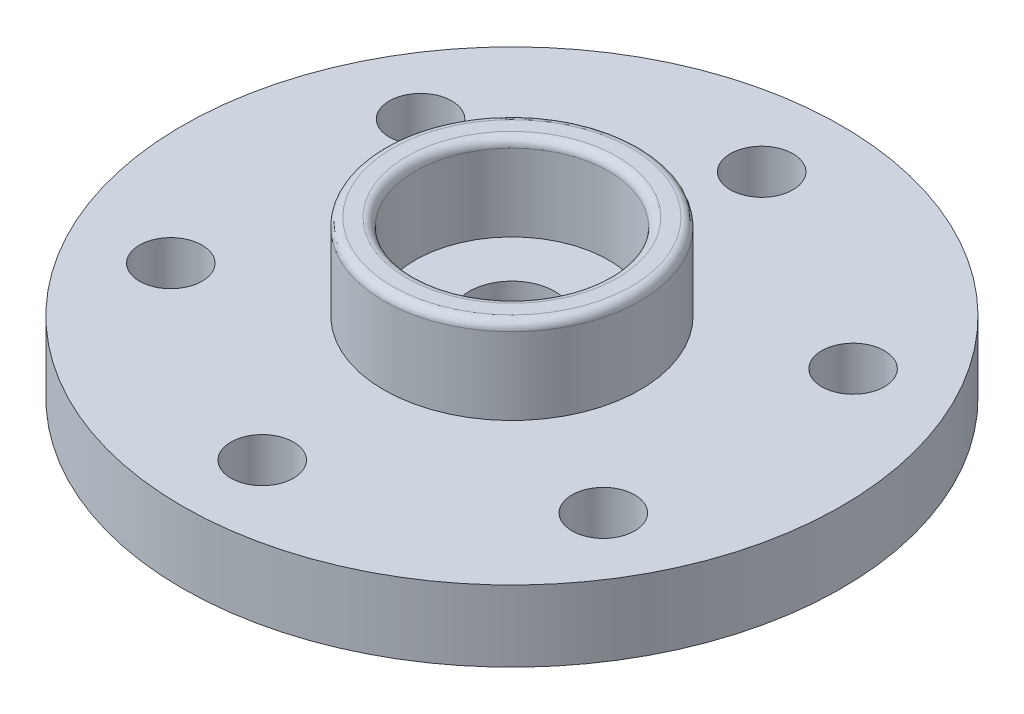
SolidWorks part; units mm, degrees
ref_plane "Alzado" through (0, 0, 0) normal (0, 0, 1) x (1, 0, 0)
ref_plane "Planta" through (0, 0, 0) normal (0, 1, 0) x (1, 0, 0)
ref_plane "Vista lateral" through (0, 0, 0) normal (1, 0, 0) x (0, 0, -1)
sketch "Croquis1" plane through (0, 0, 0) normal (0, 1, 0) x (1, 0, 0)
  line L1 (0, 0) -> (0, -16) construction
  circle A6 centre (0, 0) radius 11.575
  circle A8 centre (0, 0) radius 7.5 construction
  point P35 (0, 0)
  point P37 (0, 0)
  dimension "D1" = 23.15
  dimension "D2" = 15
extrude "Saliente-Extruir1" add sketch "Croquis1" along normal blind 2.5
sketch "Croquis2" plane through (0, 2.5, 0) normal (0, 1, 0) x (1, 0, 0)
  circle A0 centre (0, 0) radius 4.5
  circle A1 centre (0, 0) radius 3.4
  dimension "D1" = 9
  dimension "D2" = 6.8
extrude "Saliente-Extruir2" add sketch "Croquis2" along normal blind 3
sketch "Croquis3" plane through (0, 0, 0) normal (0, -1, 0) x (1, 0, 0)
  circle A0 centre (0, 0) radius 1.5
  dimension "D1" = 3
extrude "Cortar-Extruir1" cut sketch "Croquis3" against normal up to next
sketch "Croquis4" plane through (0, 0, 0) normal (0, -1, 0) x (1, 0, 0)
  circle A0 centre (0, 0) radius 2.8
  dimension "D1" = 5.6
extrude "Cortar-Extruir2" cut sketch "Croquis4" against normal offset from surface (1 mm away) 1.5 up to face at (0, 2.5, 1.5)
sketch "Croquis5" plane through (0, 0, 0) normal (0, -1, 0) x (1, 0, 0)
  circle A0 centre (0, 0) radius 4.5
  circle A1 centre (0, 0) radius 3.5
  dimension "D1" = 9
  dimension "D2" = 7
extrude "Cortar-Extruir3" cut sketch "Croquis5" against normal blind 0.5
fillet "Redondeo1" radius 0.3 5 edges at (0, 0, -4.5) (0, 0, -2.8) (0, 0, -3.5) (0, 5.5, 3.4) (0, 5.5, 4.5)
sketch "Croquis6" plane through (0, 0, 0) normal (0, -1, 0) x (1, 0, 0)
  line L0 (0, 0) -> (0, -9.6724) construction
  circle A3 centre (0, 0) radius 8.771 construction
  circle A7 centre (0, -8.771) radius 1.1
  dimension "D4" = 17.542
extrude "Cortar-Extruir4" cut sketch "Croquis6" against normal up to next (2.5 mm away)
pattern_circular "MatrizC1" count 6 over 360 about axis through (0, 0, 0) along (0, 1, 0) of "Cortar-Extruir4"
